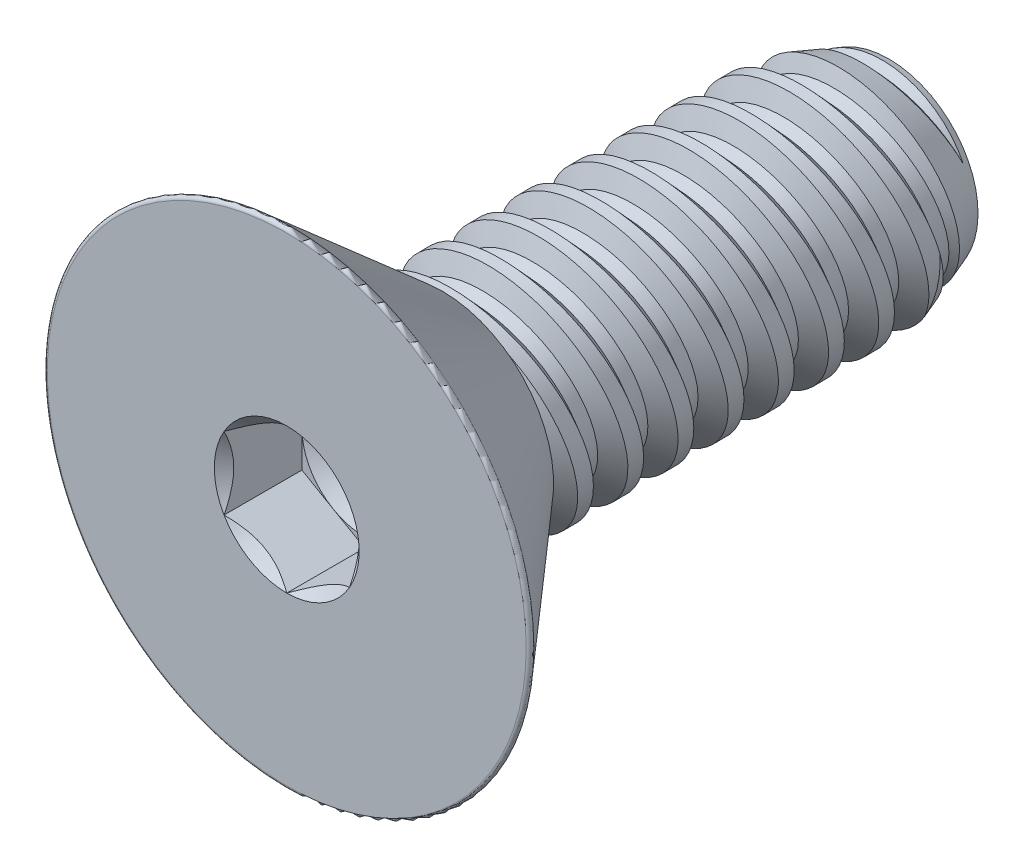
SolidWorks part; units mm, degrees
material "Alloy Steel"
ref_plane "Front" through (0, 0, 0) normal (0, 0, 1) x (1, 0, 0)
ref_plane "Top" through (0, 0, 0) normal (0, 1, 0) x (1, 0, 0)
ref_plane "Right" through (0, 0, 0) normal (1, 0, 0) x (0, 0, -1)
sketch "Sketch1" plane through (0, 0, 0) normal (1, 0, 0) x (0, 0, -1)
  line L0 (0, 0) -> (-2.4638, 0) construction
  line L1 (0, 0) -> (7.0612, 0)
  line L2 (0, 0) -> (0, 1.7526)
  line L3 (0, 1.7526) -> (7.0612, 1.7526)
  line L4 (7.0612, 0) -> (7.0612, 1.7526)
  line L5 (0, -1.7526) -> (7.0612, -1.7526) construction
  dimension "D1" = 7.0612
  dimension "Thread Dia" = 3.5052
  dimension "Length" = 9.525
  dimension "Head Height" = 2.4638
revolve "Revolve1" add sketch "Sketch1" angle 360 about L0
ref_plane "Plane1" through (0, 0, 2.4638) normal (0, 0, 1) x (1, 0, 0)
sketch "Sketch2" plane through (0, 0, 0) normal (1, 0, 0) x (0, 0, -1)
  line L0 (0, 1.7526) -> (0, -1.7526) construction
  line L1 (0, -1.7526) -> (0.7938, -1.7526) construction
  line L2 (0.7938, -1.7526) -> (0, 1.7526) construction
  line L3 (0, 1.7526) -> (0.0968, 1.7745) construction
  line L4 (0.0968, 1.7745) -> (0.7741, 1.9279)
  line L5 (0.7741, 1.9279) -> (0.6271, 1.4541)
  line L6 (0.6271, 1.4541) -> (0.4336, 1.4103)
  line L7 (0.4336, 1.4103) -> (0.0968, 1.7745)
  line L8 (0.5303, 1.4322) -> (0.4355, 1.8512) construction
  line L9 (0, -1.7526) -> (7.0612, -1.7526) construction
  line L10 (0, 1.7526) -> (7.0612, 1.7526) construction
  line L12 (0.4578, 1.7526) -> (1.2515, -1.7526) construction
  line L13 (0, -0.1935) -> (1.7093, 0.1935) construction
  line L15 (0, 0) -> (0, 1.7526) construction
  point P19 (0.8547, 0)
  dimension "D1" = 60
  dimension "Thread Pitch" = 0.7937
  dimension "D2" = 0.0992
  dimension "D3" = 0.1984
  dimension "D4" = 0.7937
revolve "Cut-Revolve1" cut sketch "Sketch2" angle 360 about L13
sketch "Sketch3" plane through (0, 0, 0) normal (1, 0, 0) x (0, 0, -1)
  line L0 (7.0612, 1.4103) -> (6.1207, 1.7526)
  line L1 (6.1207, 1.7526) -> (7.0612, 1.7526)
  line L2 (7.0612, 1.7526) -> (7.0612, 1.4103)
  line L3 (0, 1.7526) -> (7.0612, 1.7526) construction
  line L4 (7.0612, 0) -> (7.0612, 1.7526) construction
  line L5 (6.1207, 0) -> (0, 0) construction
  line L6 (6.1207, 1.7526) -> (6.1207, -1.7526) construction
  line L7 (0, -1.7526) -> (7.0612, -1.7526) construction
  dimension "D1" = 20
  dimension "D2" = 3.5052
revolve "Cut-Revolve2" cut sketch "Sketch3" angle 360 about L5
pattern_linear "LPattern1" count 9 spacing 0.7937 along (0, 0, 1)
pattern_linear "LPattern2" count 2 spacing 0.7937 along (0, 0, 1)
sketch "Sketch4" plane through (0, 0, 0) normal (0, 0, 1) x (1, 0, 0)
  circle A0 centre (0, 0) radius 3.8989
  dimension "Head Dia" = 7.7978
extrude "Extrude1" add sketch "Sketch4" along normal up to surface (2.4638 mm away)
sketch "Sketch9" plane through (0, 0, 0) normal (1, 0, 0) x (0, 0, -1)
  line L0 (-2.4638, 3.8989) -> (0, 1.7572)
  line L1 (0, 1.7572) -> (0, 3.8989)
  line L2 (0, 3.8989) -> (-2.4638, 3.8989)
  line L3 (0, 0) -> (-2.4638, 0) construction
  line L6 (-2.4638, -3.8989) -> (0, -1.7572) construction
  line L7 (0, -3.8989) -> (0, 3.8989) construction
  line L8 (-2.4638, 3.8989) -> (-2.4638, -3.8989) construction
  line L9 (0, 3.8989) -> (-2.4638, 3.8989) construction
  dimension "D1" = 82
revolve "Cut-Revolve3" cut sketch "Sketch9" angle 360 about L3
fillet "Fillet1" radius 0.0508
sketch "Sketch6" plane through (0, 0, 2.4638) normal (0, 0, 1) x (1, 0, 0)
  line L1 (0, -1.1457) -> (0.9922, -0.5728)
  line L2 (0.9922, -0.5728) -> (0.9922, 0.5728)
  line L3 (0.9922, 0.5728) -> (0, 1.1457)
  line L4 (0, 1.1457) -> (-0.9922, 0.5728)
  line L5 (-0.9922, 0.5728) -> (-0.9922, -0.5728)
  line L6 (-0.9922, -0.5728) -> (0, -1.1457)
  circle A0 centre (0, 0) radius 0.9922 construction
  dimension "Hex" = 1.9844
extrude "Cut-Extrude1" cut sketch "Sketch6" against normal blind 1.2319
sketch "Sketch7" plane through (0, 0, 2.4638) normal (0, 0, 1) x (1, 0, 0)
  circle A0 centre (0, 0) radius 1.1457
extrude "Cut-Extrude4" cut sketch "Sketch7" against normal blind 1.2319 draft 45
sketch "Sketch8" plane through (0, 0, 1.2319) normal (0, 0, 1) x (1, 0, 0)
  circle A0 centre (0, 0) radius 0.9922 construction
  circle A1 centre (0, 0) radius 0.9922
extrude "Cut-Extrude5" cut sketch "Sketch8" against normal blind 0.4106 draft 60
equation "\"D2@Sketch2\"=\"Thread Pitch@Sketch2\"/8"
equation "\"D3@Sketch2\"=\"Thread Pitch@Sketch2\"/4"
equation "\"D4@Sketch2\"=\"Thread Pitch@Sketch2\""
equation "\"D3@LPattern1\"=\"Thread Pitch@Sketch2\""
equation "\"D1@Cut-Extrude1\"=\"Head Height@Sketch1\"/2"
equation "\"D1@Cut-Extrude4\"=\"D1@Cut-Extrude1\""
equation "\"D1@Cut-Extrude5\"=\"D1@Cut-Extrude1\"/3"
equation "\"D1@LPattern1\"=\"D1@Sketch1\"/\"Thread Pitch@Sketch2\""
equation "\"D3@LPattern2\"=\"Thread Pitch@Sketch2\""
